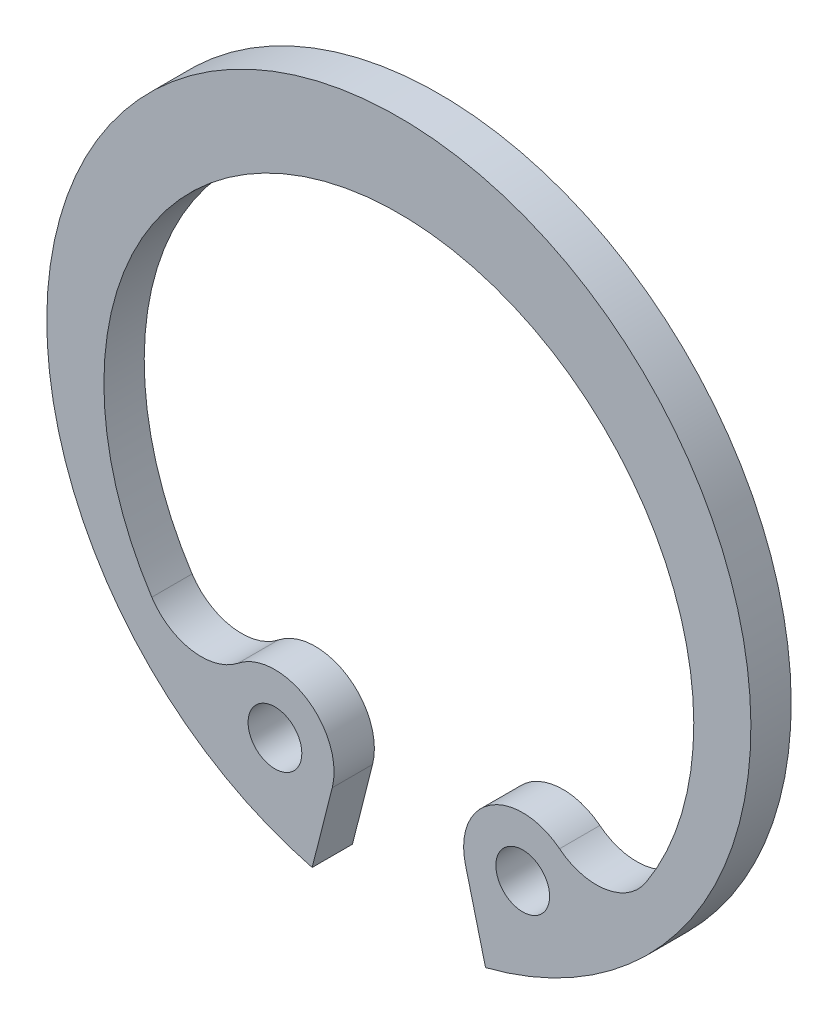
SolidWorks part; units mm, degrees
ref_plane "Plane1" through (0, 0, 0) normal (0, 0, 1) x (1, 0, 0)
ref_plane "Plane2" through (0, 0, 0) normal (0, 1, 0) x (1, 0, 0)
ref_plane "Plane3" through (0, 0, 0) normal (1, 0, 0) x (0, 0, -1)
sketch "Clipboard" plane through (0, 0, 0) normal (0, 0, 1) x (1, 0, 0)
  line L0 (0, 0) -> (3.1, 0)
  line L1 (0, 0) -> (0, 1.55)
  line L2 (0, 0) -> (0, -5)
  circle A0 centre (0, 0) radius 1
  circle A1 centre (0, 0) radius 12.5
  dimension "HoleDia" = 2
  dimension "BoreDia" = 25
  dimension "LargeSection" = 3.1
  dimension "SmallSection" = 1.55
  dimension "LugSection" = 5
sketch "BodySke" plane through (0, 0, 0) normal (0, 0, 1) x (1, 0, 0)
  line L0 (-1.5431, 0) -> (1.5431, 0) construction
  line L1 (0, 0) -> (0, 10) construction
  line L2 (3.2259, -12.6966) -> (2.4778, -9.7525)
  line L3 (-3.2259, -12.6966) -> (-2.4778, -9.7525)
  line L4 (0, 0) -> (10.3056, -8.0873) construction
  line L5 (0, 0) -> (-10.3056, -8.0873) construction
  line L6 (-4.3638, -8.2415) -> (-4.8563, -10.1799) construction
  line L7 (4.4253, -8.4832) -> (4.7949, -9.9382) construction
  arc A0 (-2.4778, -9.7525) -> (-5.9802, -7.4894) centre (-4.6101, -9.2107) ccw
  arc A1 (5.9802, -7.4894) -> (2.4778, -9.7525) centre (4.6101, -9.2107) ccw
  arc A2 (9.0862, -7.1304) -> (-9.0862, -7.1304) centre (0, -0.9749) ccw construction
  arc A3 (3.2259, -12.6966) -> (-3.2259, -12.6966) centre (0, 0) ccw
  circle A4 centre (4.6101, -9.2107) radius 1
  circle A5 centre (-4.6101, -9.2107) radius 1
  circle A6 centre (4.6101, -9.2107) radius 2.2 construction
  arc A7 (9.193, -6.9698) -> (-9.193, -6.9698) centre (0, -0.9749) ccw
  arc A8 (-4.6101, -9.2107) -> (4.6101, -9.2107) centre (0, 0) ccw construction
  arc A9 (-9.193, -6.9698) -> (-5.9802, -7.4894) centre (-7.3502, -5.7681) ccw
  arc A10 (5.9802, -7.4894) -> (9.193, -6.9698) centre (7.3502, -5.7681) ccw
  dimension "GrooveDia" = 26.2
  dimension "TipRad" = 2.2
  dimension "HoleOffsetRad" = 10.3
  dimension "HoleDia" = 2
  dimension "FilletRad" = 2.2
  dimension "LargeRad" = 10
  dimension "SmallRad" = 11.55
  dimension "SmallAngle" = 103.754
  dimension "GapAngle" = 28.511
extrude "Body" add sketch "BodySke" against normal blind 1.5
sketch "ModLugSke" plane through (0, 0, 0) normal (0, 0, 1) x (1, 0, 0)
  line L0 (3.2259, -12.6966) -> (2.0191, -7.9469)
  line L1 (-3.2259, -12.6966) -> (-2.0191, -7.9469)
  line L2 (7.0994, -3.8998) -> (11.4817, -6.3071) construction
  line L3 (-7.0994, -3.8998) -> (-11.4817, -6.3071) construction
  line L4 (-3.2259, -12.6966) -> (-2.4778, -9.7525) construction
  line L5 (2.4778, -9.7525) -> (3.2259, -12.6966) construction
  line L6 (0, 0) -> (0, -18.0732) construction
  line L7 (9.9888, -5.487) -> (11.4817, -6.3071)
  line L8 (-11.4817, -6.3071) -> (-9.9888, -5.487)
  arc A0 (3.2259, -12.6966) -> (11.4817, -6.3071) centre (0, 0) ccw
  arc A1 (-4.8943, -6.4541) -> (-2.0902, -7.8257) centre (0, 0) ccw
  arc A2 (3.2259, -12.6966) -> (-3.2259, -12.6966) centre (0, 0) ccw construction
  arc A3 (5.9802, -7.4894) -> (2.4778, -9.7525) centre (4.6101, -9.2107) ccw construction
  arc A4 (-4.8943, -6.4541) -> (-5.0179, -6.4562) centre (-4.9547, -6.5338) ccw
  arc A5 (-9.9888, -5.487) -> (-5.0179, -6.4562) centre (-7.0994, -3.8998) ccw
  arc A6 (9.193, -6.9698) -> (-9.193, -6.9698) centre (0, -0.9749) ccw construction
  arc A7 (5.0179, -6.4562) -> (9.9888, -5.487) centre (7.0994, -3.8998) ccw
  arc A8 (2.0902, -7.8257) -> (4.8943, -6.4541) centre (0, 0) ccw
  arc A9 (-11.4817, -6.3071) -> (-3.2259, -12.6966) centre (0, 0) ccw
  circle A10 centre (-4.6101, -9.2107) radius 1
  circle A11 centre (-4.6101, -9.2107) radius 1 construction
  circle A12 centre (4.6101, -9.2107) radius 1
  circle A13 centre (4.6101, -9.2107) radius 1 construction
  arc A14 (-2.0902, -7.8257) -> (-2.0191, -7.9469) centre (-2.116, -7.9223) cw
  arc A15 (2.0902, -7.8257) -> (2.0191, -7.9469) centre (2.116, -7.9223) ccw
  arc A16 (4.8943, -6.4541) -> (5.0179, -6.4562) centre (4.9547, -6.5338) cw
  point P43 (1.9946, -7.8506)
  dimension "D1" = 0.1
  dimension "LugAng" = 74.348
extrude "ModLug" [suppressed] add sketch "ModLugSke" against normal through all
sketch "UnlSke" [suppressed] plane through (0, 0, 0) normal (0, 0, 1) x (1, 0, 0)
  line L0 (1.9946, -7.8506) -> (3.2259, -12.6966)
  line L1 (-1.9946, -7.8506) -> (-3.2259, -12.6966)
  line L2 (-3.2259, -12.6966) -> (-2.0191, -7.9469) construction
  line L3 (2.0191, -7.9469) -> (3.2259, -12.6966) construction
  arc A0 (1.9946, -7.8506) -> (-1.9946, -7.8506) centre (0, 0) ccw
  arc A1 (3.2259, -12.6966) -> (-3.2259, -12.6966) centre (0, 0) ccw
  arc A2 (3.2259, -12.6966) -> (-3.2259, -12.6966) centre (0, 0) ccw construction
  circle A4 centre (-4.6101, -9.2107) radius 1
  circle A5 centre (4.6101, -9.2107) radius 1
  circle A6 centre (4.6101, -9.2107) radius 1 construction
  circle A7 centre (-4.6101, -9.2107) radius 1 construction
  arc A8 (2.0902, -7.8257) -> (4.8943, -6.4541) centre (0, 0) ccw construction
extrude "Unlug" [suppressed] add sketch "UnlSke" against normal through all
equation "' \"BoreDia@Clipboard\" = 20"
equation "' \"Thickness@Body\" = 1.5"
equation "' \"GrooveDia@BodySke\" = 21"
equation "' \"LugSection@Clipboard\" = 4.5"
equation "' \"LargeSection@Clipboard\" = 2.4"
equation "' \"HoleDia@Clipboard\" = 2"
equation "' \"BoreDia@Clipboard\" = 25"
equation "' \"GrooveDia@BodySke\" = 26.2"
equation "' \"LugSection@Clipboard\" = 5"
equation "' \"LargeSection@Clipboard\" = 3.1"
equation "\"SmallSection@Clipboard\" = \"LargeSection@Clipboard\" * 0.5"
equation "\"TipRad@BodySke\" = (\"LugSection@Clipboard\" - (\"GrooveDia@BodySke\" / 2  -  \"BoreDia@Clipboard\" / 2 ) ) / 2"
equation "\"HoleOffsetRad@BodySke\" = (\"GrooveDia@BodySke\" / 2) - \"LugSection@Clipboard\"  + \"TipRad@BodySke\""
equation "\"LargeRad@BodySke\" =  \"GrooveDia@BodySke\" / 2 -  \"LargeSection@Clipboard\""
equation "\"SmallRad@BodySke\" =  \"GrooveDia@BodySke\" / 2 -  \"SmallSection@Clipboard\""
equation "\"HoleDia@BodySke\" =  \"HoleDia@Clipboard\""
equation "\"FilletRad@BodySke\" = \"TipRad@BodySke\" * 1.0"
equation "\"GapAngle@BodySke\" = 360 - 0.965 * 360 * ( \"BoreDia@Clipboard\" /  \"GrooveDia@BodySke\")"
equation "\"LugAng@ModLugSke\" = \"GapAngle@BodySke\"  + 2 * 360 * (\"LugSection@Clipboard\" / (\"BoreDia@Clipboard\" * 3.1416))"
